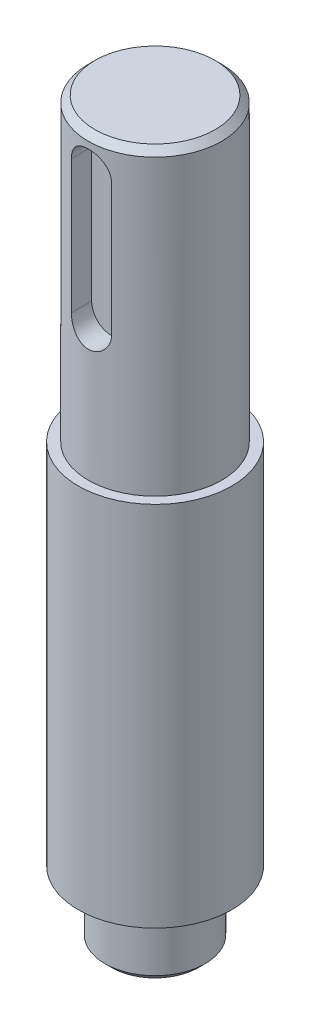
SolidWorks part; units mm, degrees
ref_plane "前视基准面" through (0, 0, 0) normal (0, 0, 1) x (1, 0, 0)
ref_plane "上视基准面" through (0, 0, 0) normal (0, 1, 0) x (1, 0, 0)
ref_plane "右视基准面" through (0, 0, 0) normal (1, 0, 0) x (0, 0, -1)
sketch "草图1" plane through (0, 0, 0) normal (0, 0, 1) x (1, 0, 0)
  line L0 (0, 0) -> (10, 0)
  line L1 (10, 0) -> (10, -45)
  line L2 (11.5, -100) -> (7.5, -100)
  line L3 (7.5, -100) -> (7.5, -110)
  line L4 (7.5, -110) -> (0, -110)
  line L5 (0, -110) -> (0, 0)
  line L6 (10, -45) -> (11.5, -45)
  line L7 (11.5, -45) -> (11.5, -100)
  dimension "D1" = 10
  dimension "D2" = 7.5
  dimension "D3" = 110
  dimension "D4" = 10
  dimension "D5" = 11.5
  dimension "D6" = 65
revolve "旋转1" add sketch "草图1" angle 360 about L5
chamfer "倒角1" distance 1 angle 45 1 edges at (0, 0, -10)
ref_plane "基准面1" through (0, 0, 6.5) normal (0, 0, 1) x (1, 0, 0)
sketch "草图2" plane through (0, 0, 6.5) normal (0, 0, 1) x (1, 0, 0)
  line L0 (0, 0) -> (0, -45) construction
  line L1 (11.5, -45) -> (-11.5, -45) construction
  line L2 (0, -5) -> (0, -25) construction
  line L3 (9, 0) -> (-9, 0) construction
  line L4 (3, -5) -> (3, -25)
  line L5 (-3, -5) -> (-3, -25)
  arc A0 (3, -5) -> (-3, -5) centre (0, -5) ccw
  arc A1 (-3, -25) -> (3, -25) centre (0, -25) ccw
  point P9 (0, -15)
  dimension "D1" = 3
  dimension "D2" = 20
  dimension "D3" = 5
extrude "切除-拉伸1" cut sketch "草图2" along normal through all
chamfer "倒角2" distance 1 angle 45 1 edges at (0, -110, -7.5)
